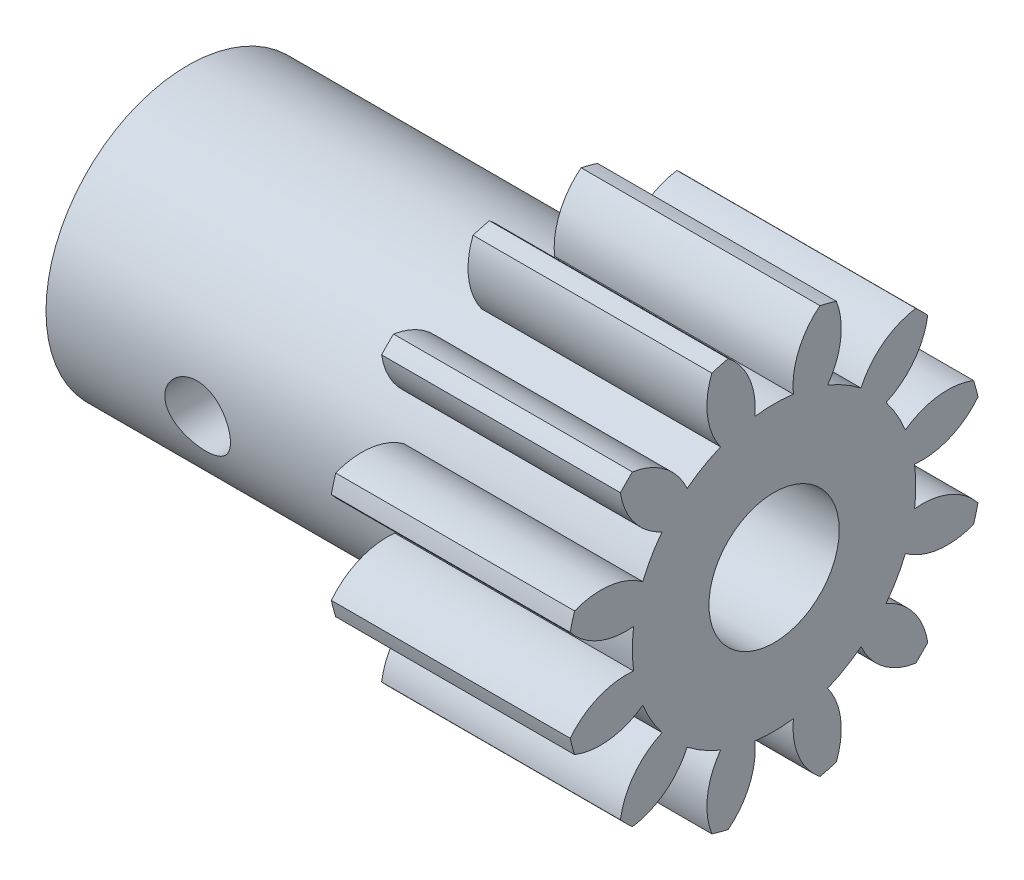
SolidWorks part; units mm, degrees
ref_plane "Front Plane" through (0, 0, 0) normal (0, 0, 1) x (1, 0, 0)
ref_plane "Top Plane" through (0, 0, 0) normal (0, 1, 0) x (1, 0, 0)
ref_plane "Right Plane" through (0, 0, 0) normal (1, 0, 0) x (0, 0, -1)
ref_plane "Plane1" through (10.6251, 0, 0) normal (1, 0, 0) x (0, 0, -1)
sketch "Sketch1" plane through (10.6251, 0, 0) normal (1, 0, 0) x (0, 0, -1)
  arc A0 (-3.4113, 6.8873) -> (-4.9507, 5.9986) centre (-0.9462, 0.8402) ccw
  arc A1 (-4.9507, 5.9986) -> (-7.4704, 7.9166) centre (-7.9642, 4.6538) ccw
  arc A2 (-7.4704, 7.9166) -> (-8.0226, 7.3644) centre (-0.9462, 0.8402) ccw
  arc A3 (-8.0226, 7.3644) -> (-6.1046, 4.8446) centre (-4.7598, 7.8582) ccw
  arc A4 (-6.1046, 4.8446) -> (-6.9933, 3.3052) centre (-0.9462, 0.8402) ccw
  arc A5 (-6.9933, 3.3052) -> (-10.1345, 3.7065) centre (-8.9308, 0.6338) ccw
  arc A6 (-10.1345, 3.7065) -> (-10.3367, 2.9521) centre (-0.9462, 0.8402) ccw
  arc A7 (-10.3367, 2.9521) -> (-7.4157, 1.729) centre (-7.7579, 5.0112) ccw
  arc A8 (-7.4157, 1.729) -> (-7.4157, -0.0486) centre (-0.9462, 0.8402) ccw
  arc A9 (-7.4157, -0.0486) -> (-10.3367, -1.2717) centre (-7.7579, -3.3308) ccw
  arc A10 (-10.3367, -1.2717) -> (-10.1345, -2.0261) centre (-0.9462, 0.8402) ccw
  arc A11 (-10.1345, -2.0261) -> (-6.9933, -1.6248) centre (-8.9308, 1.0466) ccw
  arc A12 (-6.9933, -1.6248) -> (-6.1046, -3.1642) centre (-0.9462, 0.8402) ccw
  arc A13 (-6.1046, -3.1642) -> (-8.0226, -5.684) centre (-4.7598, -6.1778) ccw
  arc A14 (-8.0226, -5.684) -> (-7.4704, -6.2362) centre (-0.9462, 0.8402) ccw
  arc A15 (-7.4704, -6.2362) -> (-4.9507, -4.3182) centre (-7.9642, -2.9734) ccw
  arc A16 (-4.9507, -4.3182) -> (-3.4113, -5.2069) centre (-0.9462, 0.8402) ccw
  arc A17 (-3.4113, -5.2069) -> (-3.8125, -8.3481) centre (-0.7399, -7.1444) ccw
  arc A18 (-3.8125, -8.3481) -> (-3.0581, -8.5502) centre (-0.9462, 0.8402) ccw
  arc A19 (-3.0581, -8.5502) -> (-1.835, -5.6293) centre (-5.1172, -5.9714) ccw
  arc A20 (-1.835, -5.6293) -> (-0.0574, -5.6293) centre (-0.9462, 0.8402) ccw
  arc A21 (-0.0574, -5.6293) -> (1.1657, -8.5502) centre (3.2248, -5.9714) ccw
  arc A22 (1.1657, -8.5502) -> (1.92, -8.3481) centre (-0.9462, 0.8402) ccw
  arc A23 (1.92, -8.3481) -> (1.5188, -5.2069) centre (-1.1526, -7.1444) ccw
  arc A24 (1.5188, -5.2069) -> (3.0582, -4.3182) centre (-0.9462, 0.8402) ccw
  arc A25 (3.0582, -4.3182) -> (5.578, -6.2362) centre (6.0718, -2.9734) ccw
  arc A26 (5.578, -6.2362) -> (6.1302, -5.684) centre (-0.9462, 0.8402) ccw
  arc A27 (6.1302, -5.684) -> (4.2121, -3.1642) centre (2.8674, -6.1778) ccw
  arc A28 (4.2121, -3.1642) -> (5.1009, -1.6248) centre (-0.9462, 0.8402) ccw
  arc A29 (5.1009, -1.6248) -> (8.2421, -2.0261) centre (7.0383, 1.0466) ccw
  arc A30 (8.2421, -2.0261) -> (8.4442, -1.2717) centre (-0.9462, 0.8402) ccw
  arc A31 (8.4442, -1.2717) -> (5.5233, -0.0486) centre (5.8654, -3.3308) ccw
  arc A32 (5.5233, -0.0486) -> (5.5233, 1.729) centre (-0.9462, 0.8402) ccw
  arc A33 (5.5233, 1.729) -> (8.4442, 2.9521) centre (5.8654, 5.0112) ccw
  arc A34 (8.4442, 2.9521) -> (8.2421, 3.7065) centre (-0.9462, 0.8402) ccw
  arc A35 (8.2421, 3.7065) -> (5.1009, 3.3052) centre (7.0383, 0.6338) ccw
  arc A36 (5.1009, 3.3052) -> (4.2121, 4.8446) centre (-0.9462, 0.8402) ccw
  arc A37 (4.2121, 4.8446) -> (6.1302, 7.3644) centre (2.8674, 7.8582) ccw
  arc A38 (6.1302, 7.3644) -> (5.578, 7.9166) centre (-0.9462, 0.8402) ccw
  arc A39 (5.578, 7.9166) -> (3.0582, 5.9986) centre (6.0718, 4.6538) ccw
  arc A40 (3.0582, 5.9986) -> (1.5188, 6.8873) centre (-0.9462, 0.8402) ccw
  arc A41 (1.5188, 6.8873) -> (1.92, 10.0285) centre (-1.1526, 8.8248) ccw
  arc A42 (1.92, 10.0285) -> (1.1657, 10.2306) centre (-0.9462, 0.8402) ccw
  arc A43 (1.1657, 10.2306) -> (-0.0574, 7.3097) centre (3.2248, 7.6518) ccw
  arc A44 (-0.0574, 7.3097) -> (-1.835, 7.3097) centre (-0.9462, 0.8402) ccw
  arc A45 (-1.835, 7.3097) -> (-3.0581, 10.2306) centre (-5.1172, 7.6518) ccw
  arc A46 (-3.0581, 10.2306) -> (-3.8125, 10.0285) centre (-0.9462, 0.8402) ccw
  arc A47 (-3.8125, 10.0285) -> (-3.4113, 6.8873) centre (-0.7399, 8.8248) ccw
extrude "Boss-Extrude1" add sketch "Sketch1" against normal blind 11
sketch "Sketch2" plane through (-0.3749, 0, 0) normal (-1, 0, 0) x (0, 0, 1)
  circle A0 centre (0.9462, 0.8402) radius 6.5303
extrude "Boss-Extrude2" add sketch "Sketch2" along normal blind 16.0001
hole_wizard "Ø6.0 (6) Diameter Hole1" positions "Sketch4" profile "Sketch3" hole size "Ø6.0" standard "ANSI Metric"
sketch "Sketch4" plane through (10.6251, 0, 0) normal (1, 0, 0) x (0, 0, -1)
  point P0 (-0.9462, 0.8402)
sketch "Sketch3" plane through (10.6251, 0.8402, 0.9462) normal (0, 1, 0) x (0, 0, -1)
  line L0 (0, 0) -> (0, 22.0001)
  line L1 (0, 22.0001) -> (3, 22.0001)
  line L2 (3, 22.0001) -> (3, 0)
  line L5 (3, 0) -> (0, 0)
  line L10 (0, 22.0001) -> (-3, 22.0001) construction
  line L11 (0, -6.35) -> (0, 107.95) construction
  dimension "Hole Dia." = 6
  dimension "Hole Depth" = 22.0001
  dimension "Drill Angle" = 180
sketch "Sketch6" plane through (10.6251, 0, 0) normal (1, 0, 0) x (0, 0, -1)
  circle A1 centre (-0.3991, -2.0926) radius 0.0166
extrude "Cut-Extrude1" cut sketch "Sketch6" against normal blind 80
sketch "Sketch7" plane through (10.6251, 0, 0) normal (1, 0, 0) x (0, 0, -1)
  circle A0 centre (-0.9462, 0.8402) radius 3
extrude "Cut-Extrude2" cut sketch "Sketch7" against normal blind 80
sketch "Sketch8" plane through (0, 0, 0) normal (0, 0, 1) x (1, 0, 0)
  circle A0 centre (-9.4499, 0) radius 1.5
extrude "Cut-Extrude3" cut sketch "Sketch8" against normal through all both and the other way through all
